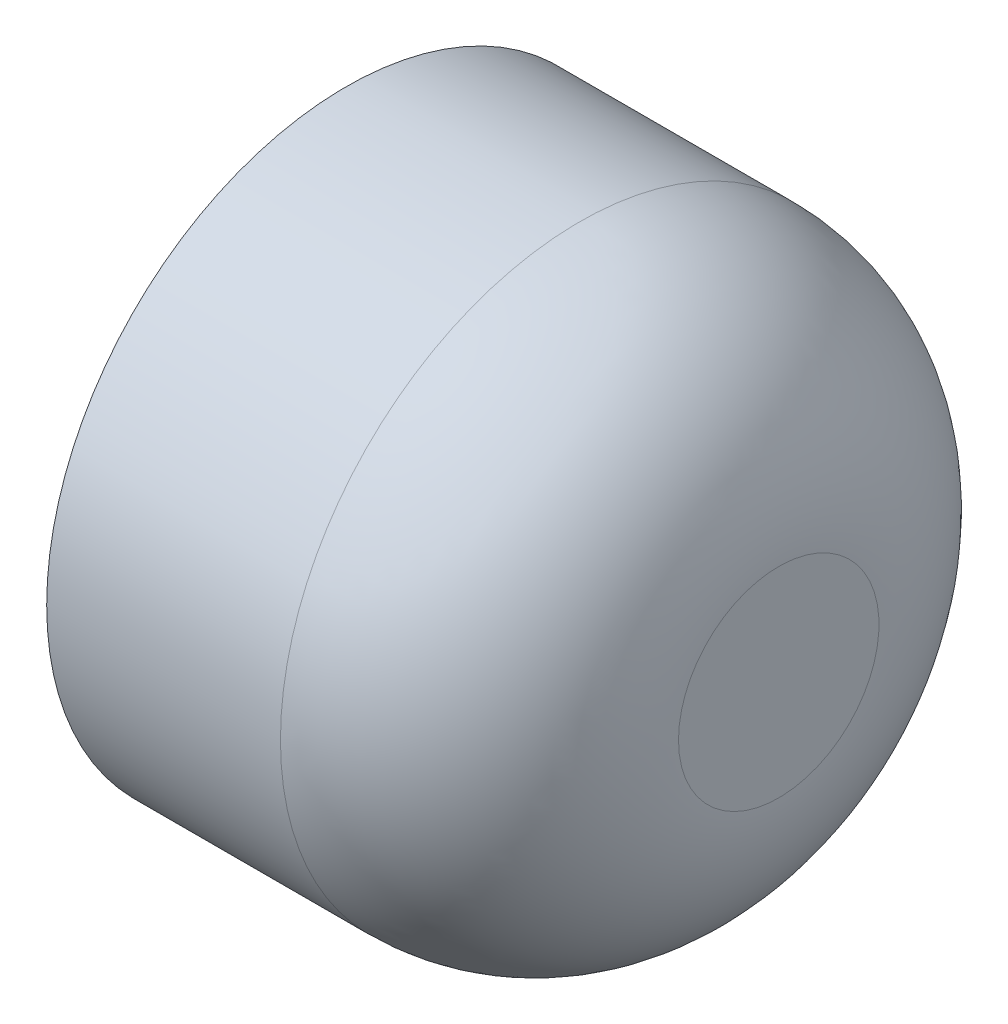
SolidWorks part; units mm, degrees
ref_plane "Front Plane" through (0, 0, 0) normal (0, 0, 1) x (1, 0, 0)
ref_plane "Top Plane" through (0, 0, 0) normal (0, 1, 0) x (1, 0, 0)
ref_plane "Right Plane" through (0, 0, 0) normal (1, 0, 0) x (0, 0, -1)
sketch "Sketch1" plane through (0, 0, 0) normal (0, 0, 1) x (1, 0, 0)
  line L0 (0, 0) -> (41.4462, 0) construction
  line L1 (-18.4618, 39.2928) -> (-18.4618, 41.4279)
  line L2 (37.6136, 0) -> (41.4462, 0)
  line L4 (-18.4618, 41.4279) -> (13.8954, 41.4279)
  line L5 (-18.4618, 41.4279) -> (-18.4618, 39.2928)
  line L7 (41.4462, 13.8771) -> (41.4462, 0)
  line L9 (-18.4618, 39.2928) -> (13.9366, 39.2928)
  line L12 (37.6136, 9.5238) -> (37.6136, 0)
  arc A1 (41.4462, 13.8771) -> (13.8954, 41.4279) centre (13.8954, 13.8771) ccw
  arc A3 (37.6136, 9.5238) -> (13.9366, 39.2928) centre (7.0608, 9.5238) ccw
  point P3 (13.057, 38.8918)
  point P5 (17.9608, 38.0661)
revolve "Revolve1" add sketch "Sketch1" angle 360 about L0
